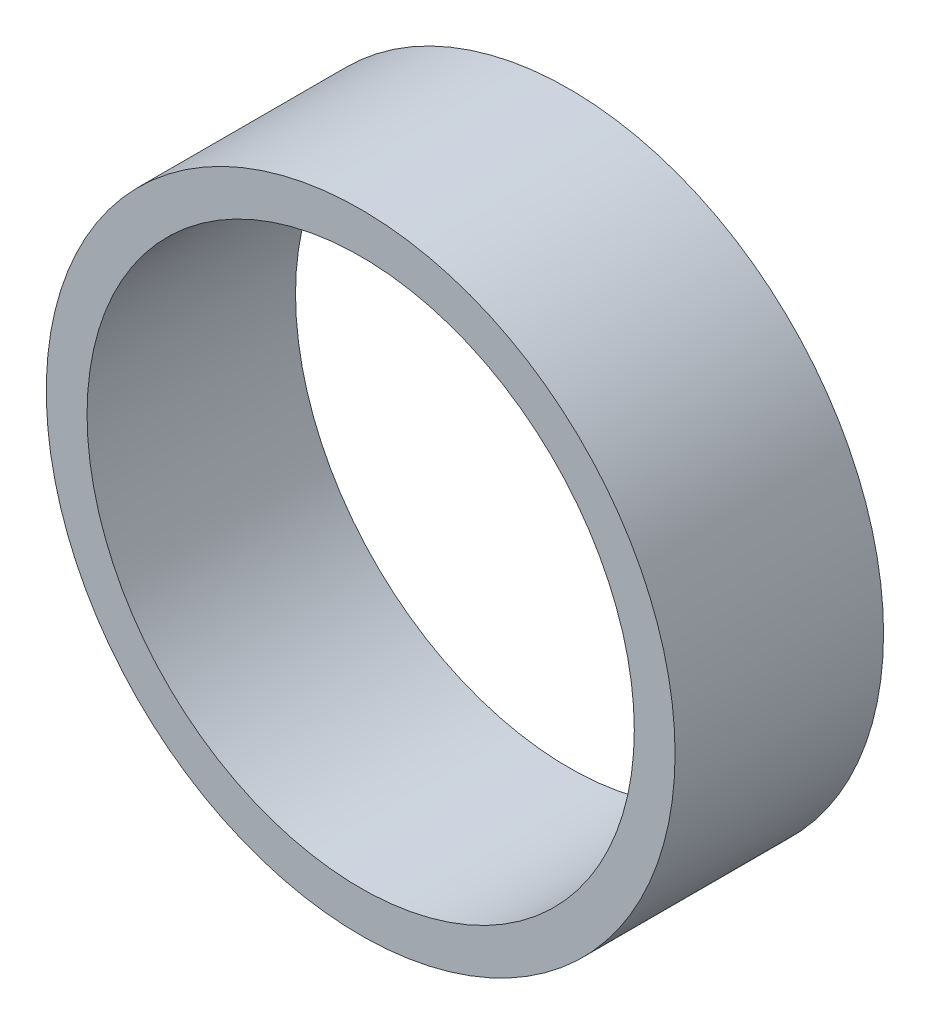
SolidWorks part; units mm, degrees
ref_plane "Front Plane" through (0, 0, 0) normal (0, 0, 1) x (1, 0, 0)
ref_plane "Top Plane" through (0, 0, 0) normal (0, 1, 0) x (1, 0, 0)
ref_plane "Right Plane" through (0, 0, 0) normal (1, 0, 0) x (0, 0, -1)
sketch "Sketch1" plane through (0, 0, 0) normal (0, 0, 1) x (1, 0, 0)
  circle A0 centre (0, 0) radius 30.1625
  dimension "Pipe OD" = 60.325
extrude "Extrude-Thin1" add sketch "Sketch1" along normal mid plane 20 thin thin type one direction reverse wall 3.9116
